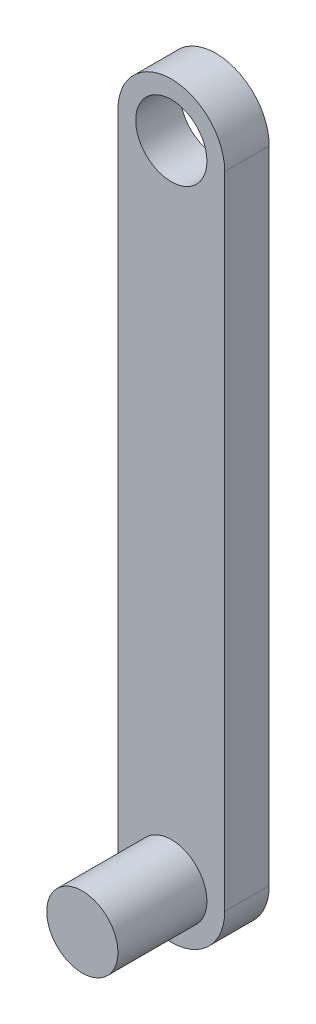
SolidWorks part; units mm, degrees
ref_plane "Front Plane" through (0, 0, 0) normal (0, 0, 1) x (1, 0, 0)
ref_plane "Top Plane" through (0, 0, 0) normal (0, 1, 0) x (1, 0, 0)
ref_plane "Right Plane" through (0, 0, 0) normal (1, 0, 0) x (0, 0, -1)
sketch "Sketch1" plane through (0, 0, 0) normal (0, 0, 1) x (1, 0, 0)
  line L0 (0, -36) -> (0, 36) construction
  line L1 (-6, -36) -> (-6, 36)
  line L2 (6, -36) -> (6, 36)
  arc A0 (-6, -36) -> (6, -36) centre (0, -36) ccw
  arc A1 (6, 36) -> (-6, 36) centre (0, 36) ccw
  circle A2 centre (0, 36) radius 4
  point P2 (0, 0)
  dimension "D2" = 6
  dimension "D3" = 8
  dimension "D1" = 72
extrude "Boss-Extrude1" add sketch "Sketch1" along normal blind 5
sketch "Sketch2" plane through (0, 0, 5) normal (0, 0, 1) x (1, 0, 0)
  circle A0 centre (0, -36) radius 4
  dimension "D1" = 8
extrude "Boss-Extrude2" add sketch "Sketch2" along normal blind 10
